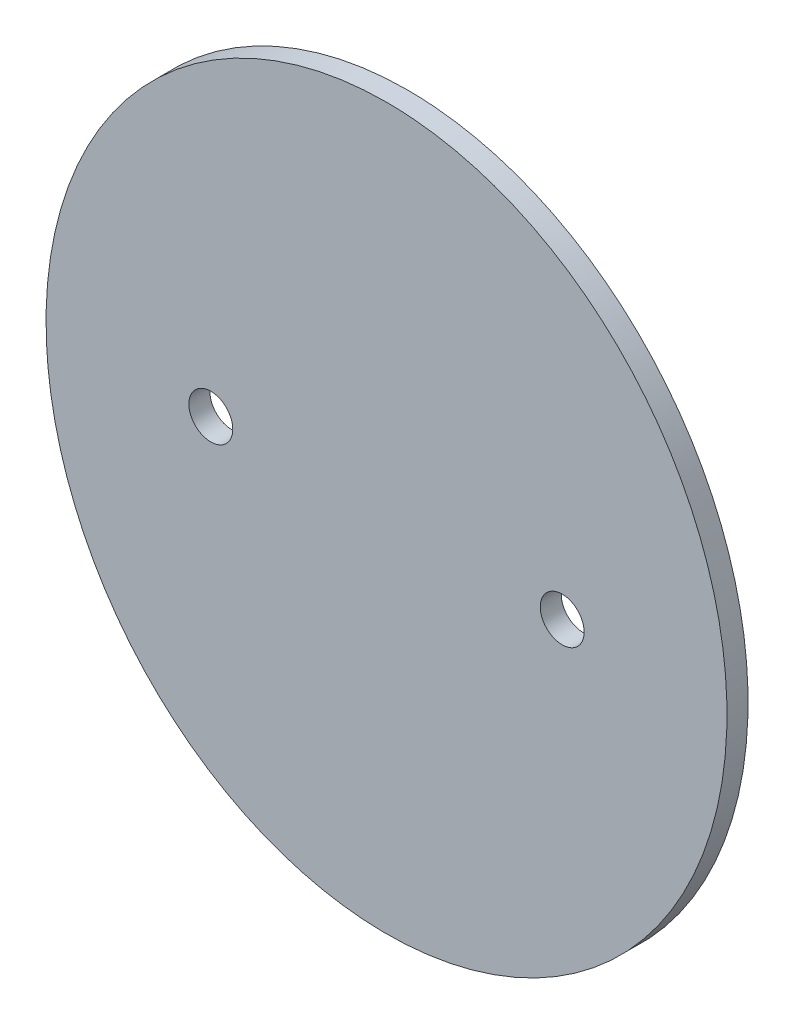
SolidWorks part; units mm, degrees
material "1060 Alloy"
ref_plane "Front Plane" through (0, 0, 0) normal (0, 0, 1) x (1, 0, 0)
ref_plane "Top Plane" through (0, 0, 0) normal (0, 1, 0) x (1, 0, 0)
ref_plane "Right Plane" through (0, 0, 0) normal (1, 0, 0) x (0, 0, -1)
sketch "Sketch1" plane through (0, 0, 0) normal (0, 0, 1) x (1, 0, 0)
  line L0 (0, -120.8333) -> (0, 115.8333) construction
  line L1 (-136.9444, 0) -> (155.2778, 0) construction
  circle A0 centre (-50, 0) radius 6.25
  circle A1 centre (50, 0) radius 6.25
  ellipse E0 centre (0, 0) end of major axis (0, 102.5) minor radius 96.9
  dimension "D3" = 100
  dimension "D4" = 12.5
  dimension "D1" = 102.5
  dimension "D2" = 96.9
extrude "Boss-Extrude1" add sketch "Sketch1" along normal blind 6
